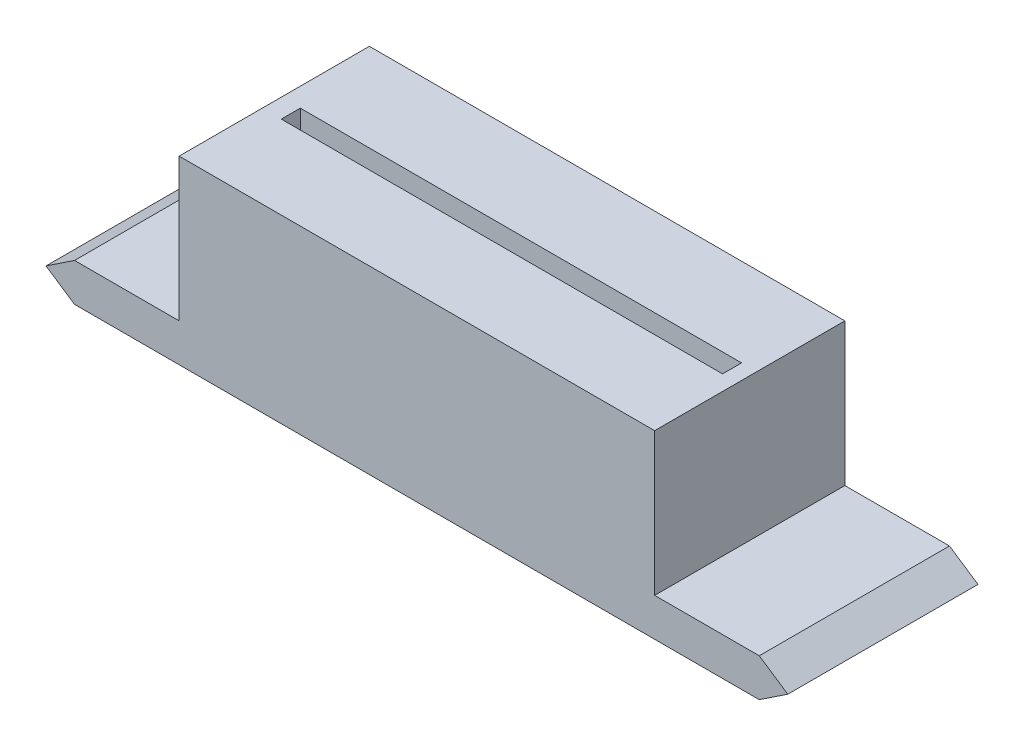
SolidWorks part; units mm, degrees
ref_plane "Přední rovina" through (0, 0, 0) normal (0, 0, 1) x (1, 0, 0)
ref_plane "Horní rovina" through (0, 0, 0) normal (0, 1, 0) x (1, 0, 0)
ref_plane "Pravá rovina" through (0, 0, 0) normal (1, 0, 0) x (0, 0, -1)
sketch "Skica1" plane through (0, 0, 0) normal (0, 0, 1) x (1, 0, 0)
  line L0 (-52.1567, -7.7147) -> (-16.1567, -7.7147)
  line L1 (-16.1567, -7.7147) -> (-14.6567, -6.7147)
  line L2 (-14.6567, -6.7147) -> (-16.1567, -5.7147)
  line L3 (-16.1567, -5.7147) -> (-21.6567, -5.7147)
  line L4 (-21.6567, -5.7147) -> (-21.6567, 1.7853)
  line L5 (-21.6567, 1.7853) -> (-46.6567, 1.7853)
  line L6 (-46.6567, 1.7853) -> (-46.6567, -5.7147)
  line L7 (-46.6567, -5.7147) -> (-52.1567, -5.7147)
  line L8 (-52.1567, -5.7147) -> (-53.6567, -6.7147)
  line L9 (-53.6567, -6.7147) -> (-52.1567, -7.7147)
  dimension "D8" = 5.5
  dimension "D1" = 36
  dimension "D4" = 5.5
  dimension "D5" = 7.5
  dimension "D6" = 25
  dimension "D7" = 7.5
extrude "Přidat vysunutím1" add sketch "Skica1" along normal blind 10 contours L9 L0 L1 L2 L3 L4 L5 L6 L7 L8
sketch "Skica2" plane through (0, -7.7147, 0) normal (0, -1, 0) x (-1, 0, 0)
  line L0 (52.1567, -10) -> (52.1567, 0) construction
  line L1 (52.1567, -10) -> (16.1567, -10) construction
  circle A0 centre (43.1567, -5) radius 3
  circle A1 centre (37.1467, -5) radius 3
  circle A2 centre (31.1367, -5) radius 3
  circle A3 centre (25.1267, -5) radius 3
  dimension "D1" = 6
  dimension "D2" = 9
  dimension "D3" = 5
  dimension "D4" = 4
extrude "Odebrat vysunutím1" cut sketch "Skica2" against normal blind 1
sketch "Skica3" plane through (0, -6.7147, 0) normal (0, -1, 0) x (-1, 0, 0)
  circle A0 centre (43.1567, -5) radius 2.6
  circle A1 centre (37.1467, -5) radius 2.6
  circle A2 centre (31.1367, -5) radius 2.6
  circle A3 centre (25.1267, -5) radius 2.6
  dimension "D1" = 5.2
  dimension "D2" = 4
extrude "Odebrat vysunutím2" cut sketch "Skica3" against normal blind 7.5
sketch "Skica4" plane through (0, 1.7853, 0) normal (0, 1, 0) x (1, 0, 0)
  line L0 (-21.6567, -10) -> (-21.6567, 0) construction
  line L1 (-45.6567, -4.6299) -> (-22.4567, -4.6299)
  line L2 (-45.6567, -4.6299) -> (-45.6567, -5.6299)
  line L3 (-45.6567, -5.6299) -> (-22.4567, -5.6299)
  line L4 (-22.4567, -4.6299) -> (-22.4567, -5.6299)
  line L5 (-45.6567, -4.6299) -> (-22.4567, -5.6299) construction
  line L6 (-45.6567, -5.6299) -> (-22.4567, -4.6299) construction
  point P0 (-34.0567, -5.1299)
  dimension "D1" = 1
  dimension "D2" = 23.2
  dimension "D3" = 0.8
extrude "Odebrat vysunutím3" cut sketch "Skica4" against normal blind 1
